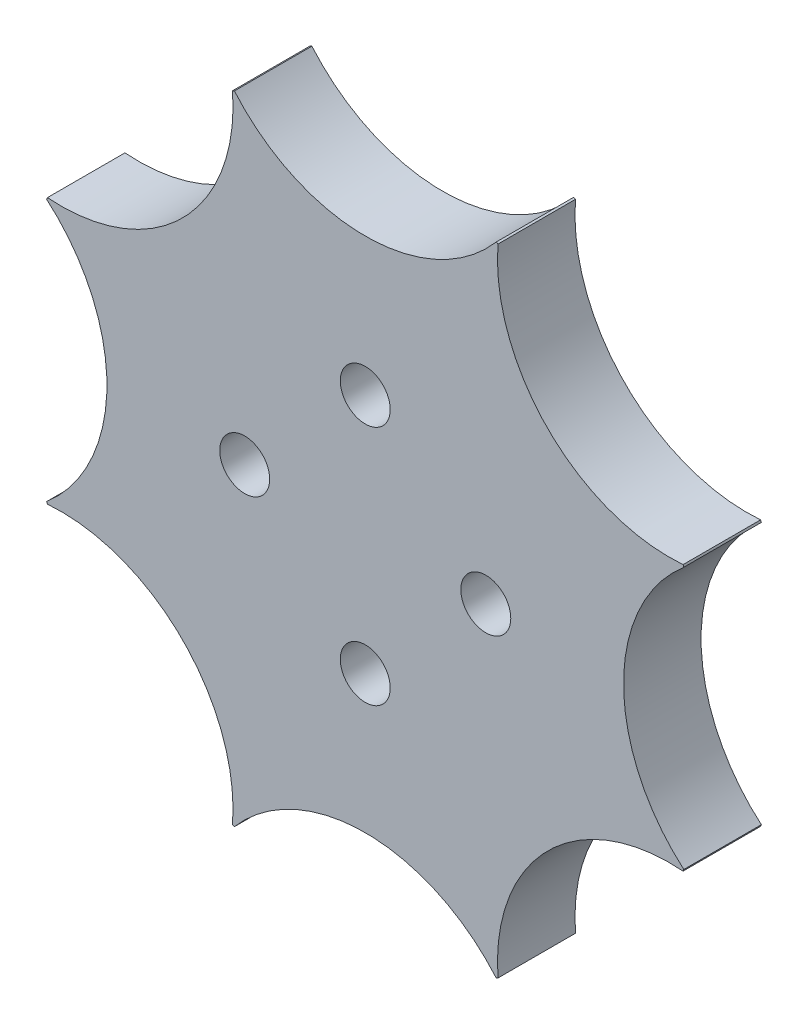
SolidWorks part; units mm, degrees
ref_plane "Front Plane" through (0, 0, 0) normal (0, 0, 1) x (1, 0, 0)
ref_plane "Top Plane" through (0, 0, 0) normal (0, 1, 0) x (1, 0, 0)
ref_plane "Right Plane" through (0, 0, 0) normal (1, 0, 0) x (0, 0, -1)
sketch "Sketch2" plane through (0, 0, 0) normal (0, 0, 1) x (1, 0, 0)
  circle A0 centre (0, 0) radius 20
  circle A1 centre (-25, 0) radius 10
  circle A2 centre (-17.6777, 17.6777) radius 10
  circle A3 centre (0, 25) radius 10
  circle A4 centre (17.6777, 17.6777) radius 10
  circle A5 centre (25, 0) radius 10
  circle A6 centre (17.6777, -17.6777) radius 10
  circle A7 centre (0, -25) radius 10
  circle A8 centre (-17.6777, -17.6777) radius 10
  point P24 (0, 0)
  dimension "D1" = 20
  dimension "D2" = 40
  dimension "D3" = 25
  dimension "D4" = 8
extrude "Boss-Extrude1" add sketch "Sketch2" along normal blind 4.5 contours A1 A0
sketch "Sketch3" plane through (0, 0, 0) normal (0, 0, 1) x (1, 0, 0)
  circle A0 centre (0, 0) radius 10.5
  dimension "D1" = 21
extrude "Cut-Extrude1" cut sketch "Sketch3" along normal blind 2
sketch "Sketch4" plane through (0, 0, 4.5) normal (0, 0, 1) x (1, 0, 0)
  circle A0 centre (0, 0) radius 7 construction
  circle A1 centre (0, 7) radius 1.45
  circle A2 centre (7, 0) radius 1.45
  circle A3 centre (0, -7) radius 1.45
  circle A4 centre (-7, 0) radius 1.45
  point P14 (0, 0)
  dimension "D1" = 14
  dimension "D2" = 2.9
  dimension "D3" = 4
extrude "Cut-Extrude2" cut sketch "Sketch4" against normal up to next
